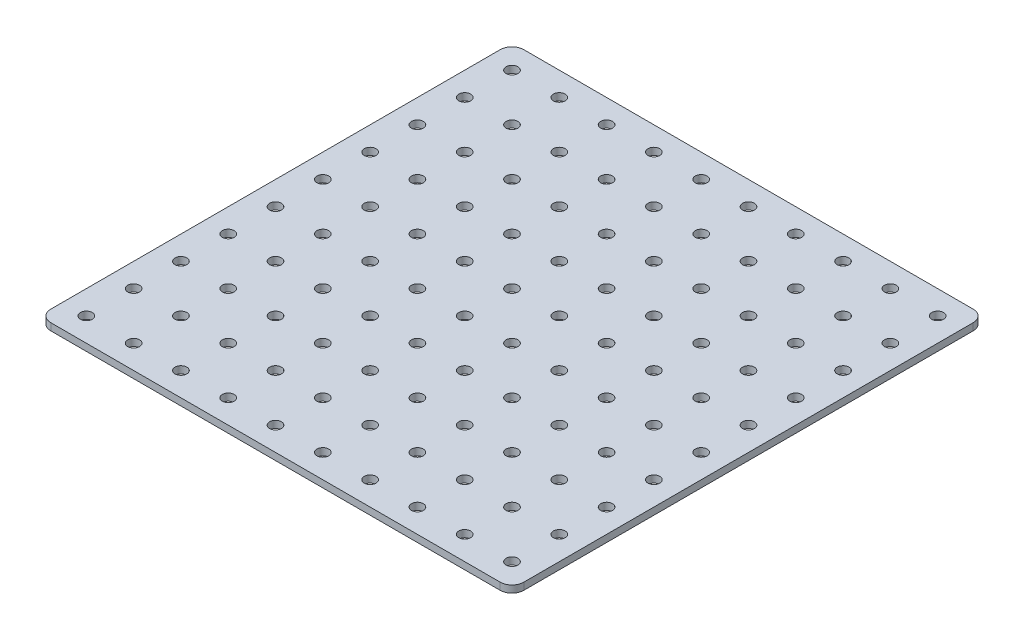
SolidWorks part; units mm, degrees
ref_plane "Front Plane" through (0, 0, 0) normal (0, 0, 1) x (1, 0, 0)
ref_plane "Top Plane" through (0, 0, 0) normal (0, 1, 0) x (1, 0, 0)
ref_plane "Right Plane" through (0, 0, 0) normal (1, 0, 0) x (0, 0, -1)
sketch "Sketch1" plane through (0, 0, 0) normal (0, 1, 0) x (1, 0, 0)
  line L1 (0, 0) -> (200, 0)
  line L2 (0, 0) -> (0, 200)
  line L3 (0, 200) -> (200, 200)
  line L4 (200, 0) -> (200, 200)
extrude "Boss-Extrude1" add sketch "Sketch1" along normal blind 3
sketch "Sketch3" plane through (0, 3, 0) normal (0, 1, 0) x (1, 0, 0)
  circle A0 centre (190, 10) radius 2.5
extrude "Cut-Extrude1" cut sketch "Sketch3" against normal through all
pattern_linear "LPattern1" count 10 spacing 20 along (0, 0, -1) count 10 spacing 20 along (-1, 0, 0) of "Cut-Extrude1"
fillet "Fillet1" radius 5 4 edges at (200, 1.5, 0) (0, 1.5, 0) (0, 1.5, -200) (200, 1.5, -200)
